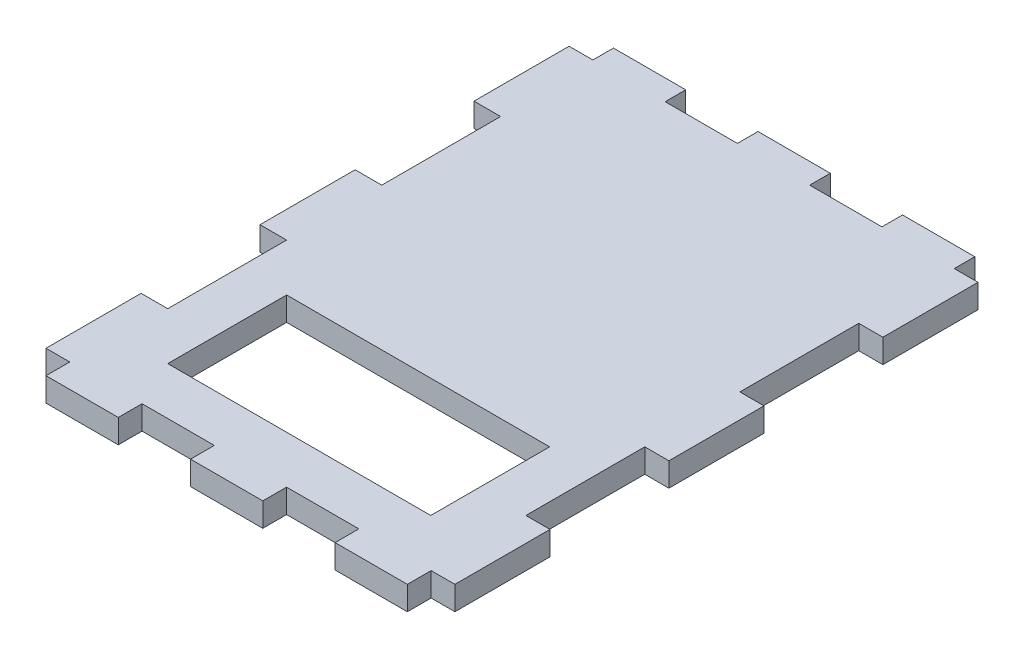
SolidWorks part; units mm, degrees
ref_plane "Front Plane" through (0, 0, 0) normal (0, 0, 1) x (1, 0, 0)
ref_plane "Top Plane" through (0, 0, 0) normal (0, 1, 0) x (1, 0, 0)
ref_plane "Right Plane" through (0, 0, 0) normal (1, 0, 0) x (0, 0, -1)
sketch "Sketch1" plane through (0, 0, 0) normal (0, 1, 0) x (1, 0, 0)
  line L0 (-101.7388, -22.0483) -> (-101.7388, -27.1283)
  line L1 (-101.7388, -27.1283) -> (-86.2988, -27.1283)
  line L2 (-86.2988, -27.1283) -> (-86.2988, -22.0483)
  line L3 (-86.2988, -22.0483) -> (-70.8588, -22.0483)
  line L4 (-70.8588, -22.0483) -> (-70.8588, -27.1283)
  line L5 (-70.8588, -27.1283) -> (-55.4188, -27.1283)
  line L6 (-55.4188, -27.1283) -> (-55.4188, -22.0483)
  line L7 (-55.4188, -22.0483) -> (-39.9788, -22.0483)
  line L8 (-39.9788, -22.0483) -> (-39.9788, -27.1283)
  line L9 (-39.9788, -27.1283) -> (-24.5388, -27.1283)
  line L10 (-24.5388, -27.1283) -> (-24.5388, -22.0483)
  line L11 (-24.5388, -22.0483) -> (-19.4588, -22.0483)
  line L12 (-19.4588, -22.0483) -> (-19.4588, -1.7283)
  line L13 (-19.4588, -1.7283) -> (-24.6146, -1.7283)
  line L14 (-24.6146, -1.7283) -> (-24.6146, 23.6717)
  line L15 (-24.6146, 23.6717) -> (-19.4588, 23.6717)
  line L16 (-19.4588, 23.6717) -> (-19.4588, 43.9917)
  line L17 (-19.4588, 43.9917) -> (-24.6146, 43.9917)
  line L18 (-24.6146, 43.9917) -> (-24.6146, 69.3917)
  line L19 (-24.6146, 69.3917) -> (-19.4588, 69.3917)
  line L20 (-19.4588, 69.3917) -> (-19.4588, 89.7117)
  line L21 (-19.4588, 89.7117) -> (-24.5388, 89.7117)
  line L22 (-24.5388, 89.7117) -> (-24.5388, 94.1093)
  line L23 (-24.5388, 94.1093) -> (-39.9788, 94.1093)
  line L24 (-39.9788, 94.1093) -> (-39.9788, 89.7117)
  line L25 (-39.9788, 89.7117) -> (-55.4188, 89.7117)
  line L26 (-55.4188, 89.7117) -> (-55.4188, 94.1093)
  line L27 (-55.4188, 94.1093) -> (-70.8588, 94.1093)
  line L28 (-70.8588, 94.1093) -> (-70.8588, 89.7117)
  line L29 (-70.8588, 89.7117) -> (-86.2988, 89.7117)
  line L30 (-86.2988, 89.7117) -> (-86.2988, 94.1093)
  line L31 (-86.2988, 94.1093) -> (-101.7388, 94.1093)
  line L32 (-101.7388, 94.1093) -> (-101.7388, 89.7117)
  line L33 (-101.7388, 89.7117) -> (-106.8188, 89.7117)
  line L34 (-106.8188, 89.7117) -> (-106.8188, 69.3917)
  line L35 (-106.8188, 69.3917) -> (-101.1322, 69.3917)
  line L36 (-101.1322, 69.3917) -> (-101.1322, 43.9917)
  line L37 (-101.1322, 43.9917) -> (-106.8188, 43.9917)
  line L38 (-106.8188, 43.9917) -> (-106.8188, 23.6717)
  line L39 (-106.8188, 23.6717) -> (-101.1322, 23.6717)
  line L40 (-101.1322, 23.6717) -> (-101.1322, -1.7283)
  line L41 (-101.1322, -1.7283) -> (-106.8188, -1.7283)
  line L42 (-106.8188, -1.7283) -> (-106.8188, -22.0483)
  line L43 (-106.8188, -22.0483) -> (-101.7388, -22.0483)
  dimension "D1" = 5.08
  dimension "D2" = 5.08
  dimension "D3" = 15.44
  dimension "D4" = 15.44
  dimension "D5" = 15.44
  dimension "D6" = 15.44
  dimension "D7" = 15.44
  dimension "D8" = 5.08
  dimension "D9" = 5.08
  dimension "D10" = 20.32
  dimension "D11" = 20.32
  dimension "D12" = 25.4
  dimension "D13" = 25.4
  dimension "D14" = 20.32
  dimension "D15" = 20.32
  dimension "D16" = 25.4
  dimension "D17" = 25.4
  dimension "D18" = 20.32
  dimension "D19" = 20.32
  dimension "D20" = 5.08
  dimension "D21" = 5.08
  dimension "D22" = 15.44
  dimension "D23" = 15.44
  dimension "D24" = 15.44
  dimension "D25" = 15.44
  dimension "D26" = 15.44
extrude "Boss-Extrude1" add sketch "Sketch1" along normal blind 5.08
sketch "Sketch5" plane through (0, 5.08, 0) normal (0, 1, 0) x (1, 0, 0)
  line L0 (-101.1322, 23.6717) -> (-101.1322, -1.7283) construction
  line L1 (-90.9722, 13.5117) -> (-34.7746, 13.5117)
  line L2 (-90.9722, 13.5117) -> (-90.9722, -11.8883)
  line L3 (-90.9722, -11.8883) -> (-34.7746, -11.8883)
  line L4 (-34.7746, 13.5117) -> (-34.7746, -11.8883)
  line L5 (-24.6146, -1.7283) -> (-24.6146, 23.6717) construction
  line L6 (-86.2988, -22.0483) -> (-70.8588, -22.0483) construction
  line L7 (-70.8588, 89.7117) -> (-86.2988, 89.7117) construction
  dimension "D1" = 10.16
  dimension "D2" = 10.16
  dimension "D3" = 10.16
  dimension "D4" = 76.2
extrude "Cut-Extrude1" cut sketch "Sketch5" against normal blind 50.8
